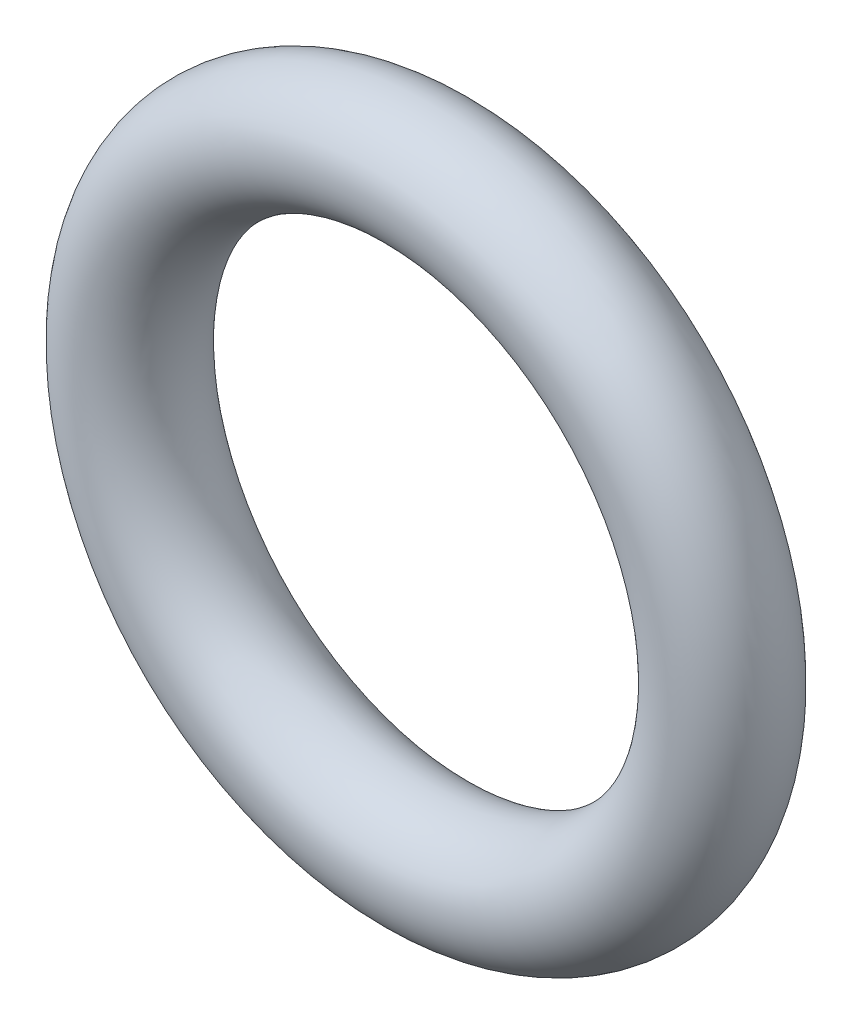
SolidWorks part; units mm, degrees
ref_plane "Front Plane" through (0, 0, 0) normal (0, 0, 1) x (1, 0, 0)
ref_plane "Top Plane" through (0, 0, 0) normal (0, 1, 0) x (1, 0, 0)
ref_plane "Right Plane" through (0, 0, 0) normal (1, 0, 0) x (0, 0, -1)
sketch "Sketch1" plane through (0, 0, 0) normal (1, 0, 0) x (0, 0, -1)
  circle A0 centre (0, 0) radius 1.6867
  dimension "D1" = 3.3734
sketch "Sketch2" plane through (0, 0, 0) normal (0, 0, 1) x (1, 0, 0)
  circle A0 centre (0, -8.4336) radius 8.4336
  dimension "D1" = 16.8672
sweep "Sweep1" add profiles "Sketch1" path "Sketch2"
ref_point "Point1" parameters "D1"=0.762
sketch "Sketch3" plane through (0, 0, 0) normal (0, 0, 1) x (1, 0, 0)
  line L0 (0, -1.6867) -> (0, -15.1805) construction
  circle A0 centre (0, -8.4336) radius 6.7469 construction
  circle A1 centre (0, -8.4336) radius 6.7469
  point P3 (-4.7625, -3.6546)
  point P4 (4.7625, -3.6546)
  point P5 (4.7625, -13.2126)
  point P6 (-4.7625, -13.2126)
  point P9 (0, 0)
  point P10 (0, 0)
  dimension "D1" = 9.525
  dimension "D2" = 9.525
ref_point "Point2"
ref_point "Point3"
ref_point "Point4"
ref_point "Point5"
sketch "Sketch4" plane through (0, 0, 0) normal (1, 0, 0) x (0, 0, -1)
  point P0 (1.6294, -17.2048)
  point P1 (0, 0)
  point P2 (0, 0)
  point P3 (0, 0)
  point P4 (1.6294, -17.2048)
ref_point "Point6"
